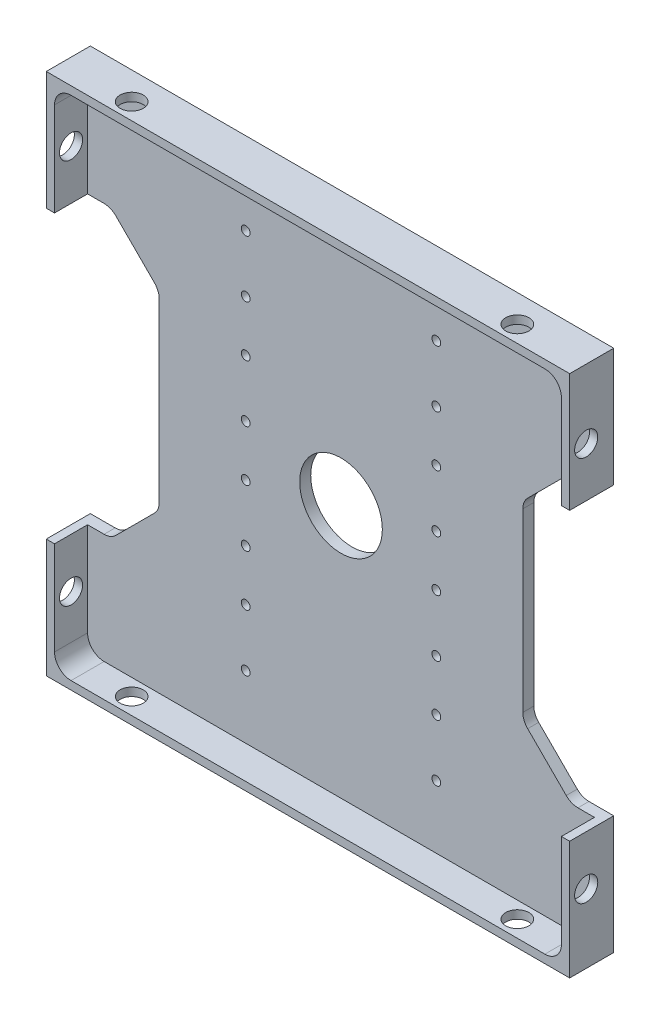
SolidWorks part; units mm, degrees
material "6061-T6 (SS)"
ref_plane "Front" through (0, 0, 0) normal (0, 0, 1) x (1, 0, 0)
ref_plane "Top" through (0, 0, 0) normal (0, 1, 0) x (1, 0, 0)
ref_plane "Right" through (0, 0, 0) normal (1, 0, 0) x (0, 0, -1)
sketch "Sketch1" plane through (0, 0, 0) normal (0, 0, 1) x (1, 0, 0)
  line L1 (-48, -48) -> (48, -48)
  line L2 (-48, -48) -> (-48, 48)
  line L3 (-48, 48) -> (48, 48)
  line L4 (48, -48) -> (48, 48)
  line L5 (-48, -48) -> (48, 48) construction
  line L6 (-48, 48) -> (48, -48) construction
  point P0 (0, 0)
  dimension "D1" = 96
  dimension "D2" = 96
extrude "Boss-Extrude1" add sketch "Sketch1" along normal blind 8
sketch "Sketch2" plane through (0, 0, 8) normal (0, 0, 1) x (1, 0, 0)
  line L1 (46, -46) -> (-46, -46)
  line L2 (46, -46) -> (46, 46)
  line L3 (46, 46) -> (-46, 46)
  line L4 (-46, -46) -> (-46, 46)
  line L5 (46, -46) -> (-46, 46) construction
  line L6 (46, 46) -> (-46, -46) construction
  point P0 (0, 0)
  dimension "D1" = 92
  dimension "D2" = 92
extrude "Component Platform" cut sketch "Sketch2" against normal blind 6
sketch "Sketch3" plane through (0, 0, 2) normal (0, 0, 1) x (1, 0, 0)
  line L1 (-40.8787, -25.1213) -> (-33.8787, -18.1213)
  line L2 (-40.8787, 25.1213) -> (-33.8787, 18.1213)
  line L3 (-33, -16) -> (-33, 16)
  line L4 (-48, -26) -> (-43, -26)
  line L7 (-48, 48) -> (-48, -48) construction
  line L8 (0, -56.7987) -> (0, 73.4321) construction
  line L9 (46, -46) -> (-57.8147, 57.8147) construction
  line L18 (46, 46) -> (-68.5705, -68.5705) construction
  line L23 (-48, 26) -> (-43, 26)
  line L26 (-48, -26) -> (-48, 26)
  line L28 (-48, -48) -> (48, -48) construction
  line L29 (48, -26) -> (48, 26)
  line L30 (48, 26) -> (43, 26)
  line L31 (40.8787, 25.1213) -> (33.8787, 18.1213)
  line L32 (33, -16) -> (33, 16)
  line L33 (40.8787, -25.1213) -> (33.8787, -18.1213)
  line L34 (48, -26) -> (43, -26)
  arc A3 (-33.8787, -18.1213) -> (-33, -16) centre (-36, -16) ccw
  arc A4 (-33.8787, 18.1213) -> (-33, 16) centre (-36, 16) cw
  arc A13 (-40.8787, -25.1213) -> (-43, -26) centre (-43, -23) cw
  arc A15 (-40.8787, 25.1213) -> (-43, 26) centre (-43, 23) ccw
  arc A17 (40.8787, 25.1213) -> (43, 26) centre (43, 23) cw
  arc A18 (33.8787, 18.1213) -> (33, 16) centre (36, 16) ccw
  arc A19 (33.8787, -18.1213) -> (33, -16) centre (36, -16) cw
  arc A20 (40.8787, -25.1213) -> (43, -26) centre (43, -23) ccw
  point P0 (-48, 0)
  point P37 (-48, 0)
  dimension "D2" = 3
  dimension "D3" = 3
  dimension "D4" = 15
  dimension "D6" = 3
  dimension "D7" = 3
  dimension "D8" = 135
  dimension "D5" = 52
  dimension "D9" = 135
  dimension "D10" = 5
  dimension "D11" = 5
  dimension "D12" = 48
extrude "Cable Slots" cut sketch "Sketch3" against normal mid plane 12
sketch "Sketch4" plane through (0, 0, 2) normal (0, 0, 1) x (1, 0, 0)
  circle A0 centre (0, 0) radius 7.5
  dimension "D1" = 15
extrude "Center Mass Cut" cut sketch "Sketch4" against normal blind 6
ref_plane "Center Y-Plane" through (0, 0, 0) normal (1, 0, 0) x (0, 0, -1)
ref_plane "Center X-Plane" through (0, 0, 0) normal (0, -1, 0) x (-1, 0, 0)
fillet "Inner Corner Fillets" radius 3 4 edges at (46, -46, 5) (-46, -46, 5) (46, 46, 5) (-46, 46, 5)
sketch "Sketch8" plane through (48, 0, 0) normal (1, 0, 0) x (0, 0, -1)
  line L0 (-5, -48) -> (-5, 48) construction
  line L1 (-8, -48) -> (0, -48) construction
  line L2 (-8, 48) -> (0, 48) construction
  line L3 (-8, -48) -> (-8, -26) construction
  point P12 (-5, 35)
  point P13 (-5, -35)
  dimension "D1" = 3
  dimension "D2" = 13
  dimension "D3" = 83
sketch "Sketch11" plane through (0, -48, 0) normal (0, -1, 0) x (-1, 0, 0)
  line L0 (48, -5) -> (-48.0639, -5) construction
  line L1 (48, -8) -> (48, 0) construction
  line L2 (48, -8) -> (-48, -8) construction
  dimension "D1" = 3
hole_wizard "Tap Drill for M5x0.8 Tap2" positions "Sketch12" profile "Sketch13" hole size "M5x0.8" standard "ANSI Metric" end condition up to next
sketch "Sketch12" plane through (0, -48, 0) normal (0, -1, 0) x (-1, 0, 0)
  line L0 (48, -5) -> (-48.0639, -5) construction
  point P0 (35, -5)
  point P4 (-35, -5)
  dimension "D1" = 70
  dimension "D2" = 35
sketch "Sketch13" plane through (-35, -48, 5) normal (1, 0, 0) x (0, 0, -1)
  line L0 (0, 0) -> (0, 2)
  line L1 (0, 2) -> (2.1, 2)
  line L2 (2.1, 2) -> (2.1, 0)
  line L5 (2.1, 0) -> (0, 0)
  line L11 (0, -6.35) -> (0, 107.95) construction
  dimension "Thru Hole Dia." = 4.2
  dimension "Thru Hole Depth" = 2
mirror "Mirror2" about plane through (0, 0, 0) normal (0, -1, 0) of "Tap Drill for M5x0.8 Tap2"
sketch "Sketch14" plane through (0, 0, 2) normal (0, 0, 1) x (1, 0, 0)
  line L2 (-34.5286, 34.575) -> (20.3487, 34.575) construction
  line L4 (-17.3, 34.575) -> (-17.3, -34.575) construction
  line L5 (0, 0) -> (0, 34.575) construction
  point P2 (-17.3, -14.975)
  point P5 (-17.3, -4.625)
  point P7 (-17.3, 34.575)
  point P8 (-17.3, 14.975)
  point P9 (-17.3, 24.225)
  point P11 (-17.3, 4.625)
  point P13 (17.3, 4.625)
  point P14 (17.3, 14.975)
  point P15 (17.3, 24.225)
  point P16 (17.3, 34.575)
  point P17 (-17.3, -24.225)
  point P18 (-17.3, -34.575)
  point P30 (17.3, -34.575)
  point P31 (17.3, -24.225)
  point P32 (17.3, -14.975)
  point P33 (17.3, -4.625)
  point P35 (-17.3, 0)
  dimension "D1" = 17.3
  dimension "D3" = 10.35
  dimension "D4" = 9.25
  dimension "D5" = 10.35
  dimension "D6" = 9.25
  dimension "D7" = 10.35
  dimension "D8" = 9.25
  dimension "D9" = 10.35
hole_wizard "Tap Drill for M2x0.4 Tap2" positions "Sketch15" profile "Sketch17" hole size "M2x0.4" standard "ANSI Metric" end condition through all
sketch "Sketch15" plane through (0, 0, 2) normal (0, 0, 1) x (1, 0, 0)
  point P0 (-17.3, 34.575)
  point P3 (-17.3, 24.225)
  point P6 (-17.3, 14.975)
  point P9 (-17.3, 4.625)
  point P12 (17.3, 4.625)
  point P15 (17.3, 14.975)
  point P18 (17.3, 24.225)
  point P21 (17.3, 34.575)
  point P46 (17.3, -4.625)
  point P49 (17.3, -14.975)
  point P52 (17.3, -24.225)
  point P55 (17.3, -34.575)
  point P58 (-17.3, -4.625)
  point P61 (-17.3, -14.975)
  point P64 (-17.3, -24.225)
  point P67 (-17.3, -34.575)
sketch "Sketch17" plane through (-17.3, 34.575, 2) normal (1, 0, 0) x (0, -1, 0)
  line L0 (0, 0) -> (0, 2)
  line L1 (0, 2) -> (0.8, 2)
  line L2 (0.8, 2) -> (0.8, 0)
  line L5 (0.8, 0) -> (0, 0)
  line L11 (0, -6.35) -> (0, 107.95) construction
  dimension "Thru Hole Dia." = 1.6
  dimension "Thru Hole Depth" = 2
hole_wizard "Tap Drill for M5x0.8 Tap1" positions "Sketch26" profile "Sketch27" hole size "M5x0.8" standard "ANSI Metric" end condition up to next
sketch "Sketch26" plane through (48, 0, 0) normal (1, 0, 0) x (0, 0, -1)
  point P0 (-5, -35)
  point P3 (-5, 35)
sketch "Sketch27" plane through (48, -35, 5) normal (0, 1, 0) x (0, 0, -1)
  line L0 (0, 0) -> (0, 2)
  line L1 (0, 2) -> (2.1, 2)
  line L2 (2.1, 2) -> (2.1, 0)
  line L5 (2.1, 0) -> (0, 0)
  line L11 (0, -6.35) -> (0, 107.95) construction
  dimension "Thru Hole Dia." = 4.2
  dimension "Thru Hole Depth" = 2
mirror "Mirror3" about plane through (0, 0, 0) normal (1, 0, 0) of "Tap Drill for M5x0.8 Tap1"
sketch "Sketch28" plane through (0, 0, 0) normal (0, 0, -1) x (-1, 0, 0)
  line L1 (47.5, -47.5) -> (-47.5, -47.5)
  line L2 (47.5, -47.5) -> (47.5, 47.5)
  line L3 (47.5, 47.5) -> (-47.5, 47.5)
  line L4 (-47.5, -47.5) -> (-47.5, 47.5)
  line L5 (47.5, -47.5) -> (-47.5, 47.5) construction
  line L6 (47.5, 47.5) -> (-47.5, -47.5) construction
  point P0 (0, 0)
  dimension "D1" = 95
  dimension "D2" = 95
extrude "Cut-Extrude1" cut sketch "Sketch28" against normal up to next flip side to cut
equation "\"MountingBracketXYSideTolerance\"= - 0.5"
equation "\"D2@Sketch28\"=96mm + \"MountingBracketXYSideTolerance\"*2"
equation "\"D1@Sketch28\"=96.00mm+\"MountingBracketXYSideTolerance\"*2"
